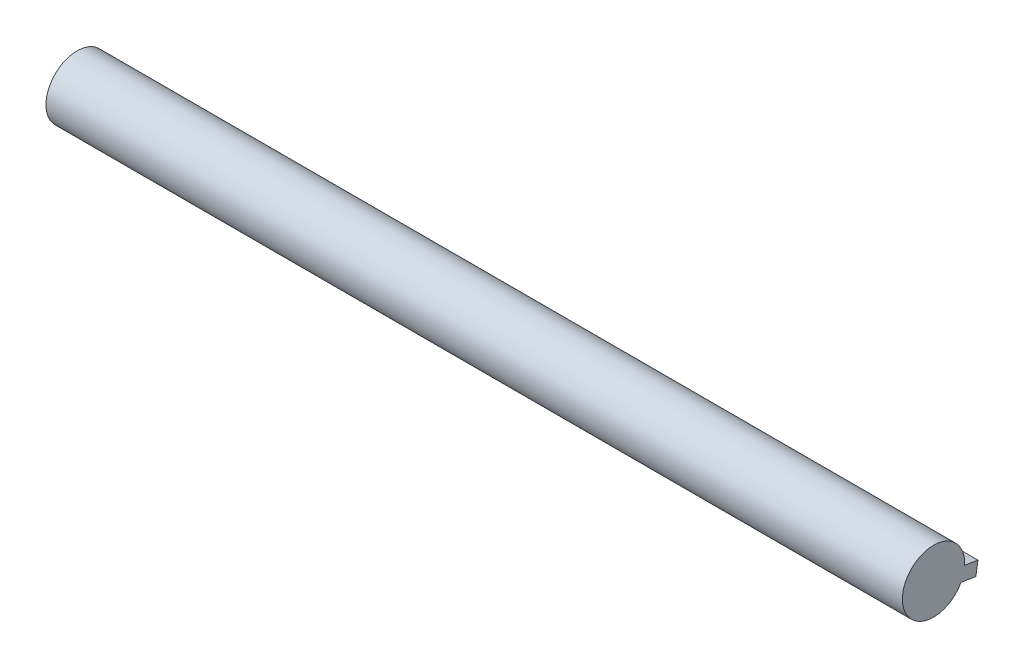
SolidWorks part; units mm, degrees
ref_plane "Front Plane" through (0, 0, 0) normal (0, 0, 1) x (1, 0, 0)
ref_plane "Top Plane" through (0, 0, 0) normal (0, 1, 0) x (1, 0, 0)
ref_plane "Right Plane" through (0, 0, 0) normal (1, 0, 0) x (0, 0, -1)
sketch "Sketch1" plane through (0, 0, 0) normal (1, 0, 0) x (0, 0, -1)
  circle A0 centre (0, 0) radius 7
  dimension "D1" = 14
extrude "Boss-Extrude1" add sketch "Sketch1" along normal blind 192.48
ref_plane "Plane1" through (0, -1.1309, -6.9081) normal (0, -0.1616, -0.9869) x (1, 0, 0)
sketch "Sketch2" plane through (0, -1.1309, -6.9081) normal (0, -0.1616, -0.9869) x (1, 0, 0)
  line L0 (192.48, -7) -> (192.48, 7) construction
  line L1 (192.48, 2.2633) -> (177.48, 2.2633)
  line L2 (192.48, 2.2633) -> (192.48, -0.7367)
  line L3 (192.48, -0.7367) -> (177.48, -0.7367)
  line L4 (177.48, 2.2633) -> (177.48, -0.7367)
  line L5 (0, 7) -> (0, -7) construction
  line L6 (0, 1.8281) -> (16.7302, 1.8281)
  line L7 (0, 1.8281) -> (0, -0.7367)
  line L8 (0, -0.7367) -> (16.7302, -0.7367)
  line L9 (16.7302, 1.8281) -> (16.7302, -0.7367)
  dimension "D1" = 15
  dimension "D2" = 3
extrude "Boss-Extrude2" add sketch "Sketch2" along normal blind 3 separate body
sketch "Sketch3" plane through (0, -1.1309, -6.9081) normal (0, 0.1616, 0.9869) x (1, 0, 0)
  line L0 (16.7302, 0.7367) -> (16.7302, -1.8281) construction
  line L1 (0, 0.7367) -> (16.7302, 0.7367)
  line L2 (0, 0.7367) -> (0, -1.8281)
  line L3 (0, -1.8281) -> (16.7302, -1.8281)
  line L4 (16.7302, 0.7367) -> (16.7302, -1.8281)
extrude "Boss-Extrude3" add sketch "Sketch3" along normal blind 10
sketch "Sketch4" plane through (0, -1.1309, -6.9081) normal (0, 0.1616, 0.9869) x (1, 0, 0)
  line L1 (192.48, -2.2633) -> (177.48, -2.2633)
  line L2 (192.48, -2.2633) -> (192.48, 0.7367)
  line L3 (192.48, 0.7367) -> (177.48, 0.7367)
  line L4 (177.48, -2.2633) -> (177.48, 0.7367)
extrude "Boss-Extrude4" add sketch "Sketch4" along normal blind 10
